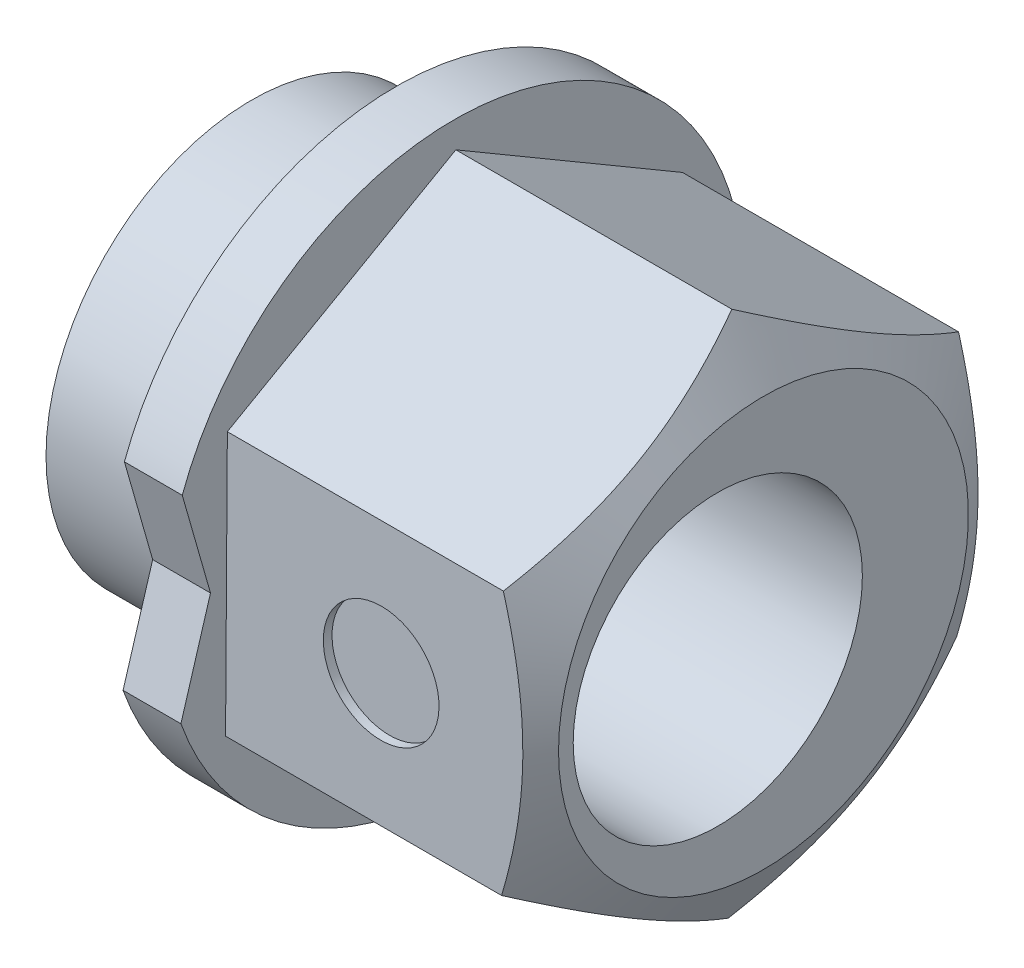
SolidWorks part; units mm, degrees
material "Chrome Stainless Steel"
ref_plane "Front Plane" through (0, 0, 0) normal (0, 0, 1) x (1, 0, 0)
ref_plane "Top Plane" through (0, 0, 0) normal (0, 1, 0) x (1, 0, 0)
ref_plane "Right Plane" through (0, 0, 0) normal (1, 0, 0) x (0, 0, -1)
sketch "Sketch2" plane through (0, 0, 0) normal (1, 0, 0) x (0, 0, -1)
  line L1 (3.9194, -2.2986) -> (3.9504, 2.245)
  line L2 (3.9504, 2.245) -> (0.0309, 4.5436)
  line L3 (0.0309, 4.5436) -> (-3.9194, 2.2986)
  line L4 (-3.9194, 2.2986) -> (-3.9504, -2.245)
  line L5 (-3.9504, -2.245) -> (-0.0309, -4.5436)
  line L6 (-0.0309, -4.5436) -> (3.9194, -2.2986)
  circle A0 centre (0, 0) radius 3.935 construction
  dimension "D1" = 7.87
extrude "Boss-Extrude1" add sketch "Sketch2" along normal blind 5.35
sketch "Sketch6" plane through (0, 0, 0) normal (-1, 0, 0) x (0, 0, 1)
  line L0 (4.6992, 1.7371) -> (4.2108, 0.0287)
  line L1 (5.7224, -1.6698) -> (5.6992, 1.74) construction
  line L2 (4.2108, 0.0287) -> (4.7224, -1.6729)
  line L3 (4.6992, 1.7371) -> (4.7224, -1.6729) construction
  line L4 (3.9194, 2.2986) -> (3.9504, -2.245) construction
  arc A0 (4.6992, 1.7371) -> (4.7224, -1.6729) centre (0, 0) ccw
  dimension "D1" = 10.02
  dimension "D2" = 3.41
  dimension "D3" = 1.5
  dimension "D4" = 1
extrude "Boss-Extrude3" add sketch "Sketch6" along normal blind 1
sketch "Sketch4" plane through (-1, 0, 0) normal (-1, 0, 0) x (0, 0, 1)
  circle A0 centre (0, 0) radius 3.555
  dimension "D1" = 7.11
extrude "Boss-Extrude4" add sketch "Sketch4" along normal blind 2.5
sketch "Sketch3" plane through (-3.5, 0, 0) normal (-1, 0, 0) x (0, 0, 1)
  line L0 (0, 0) -> (0.79, 0) construction
  circle A0 centre (0.79, 0) radius 2.5
  dimension "D1" = 5
  dimension "D2" = 0.79
sketch "Sketch5" plane through (0, 0.0268, 3.9349) normal (0, -0.0068, -1) x (1, 0, 0)
  line L1 (5.35, 0) -> (0, 0) construction
  line L2 (5.35, -2.2719) -> (5.35, 2.2719) construction
  line L3 (0, -2.2719) -> (0, 2.2719) construction
  circle A0 centre (2.675, 0) radius 1
  dimension "D1" = 2
extrude "Cut-Extrude3" cut sketch "Sketch5" along normal blind 0.15
extrude "Cut-Extrude5" cut sketch "Sketch3" against normal through all
sketch "Sketch7" plane through (0, 0, 0) normal (0, 0, 1) x (1, 0, 0)
  line L0 (4.7726, 4.5436) -> (5.35, 3.5436)
  line L1 (9.7726, 8.5436) -> (4.7726, 8.5436)
  line L2 (9.7726, 8.5436) -> (9.7726, 3.5436)
  line L3 (9.7726, 3.5436) -> (5.35, 3.5436)
  line L4 (4.7726, 8.5436) -> (4.7726, 4.5436)
  line L5 (5.35, 2.245) -> (5.35, 4.5436) construction
  line L6 (4.7726, 4.5436) -> (9.7726, 4.5436) construction
  line L7 (5.35, 4.5436) -> (0, 4.5436) construction
  dimension "D1" = 150
  dimension "D2" = 1
  dimension "D3" = 5
  dimension "D4" = 5
ref_axis "Axis1" through (0, 0, 0) along (1, 0, 0)
revolve "Cut-Revolve1" cut sketch "Sketch7" angle 360 about axis through (0, 0, 0) along (1, 0, 0)
